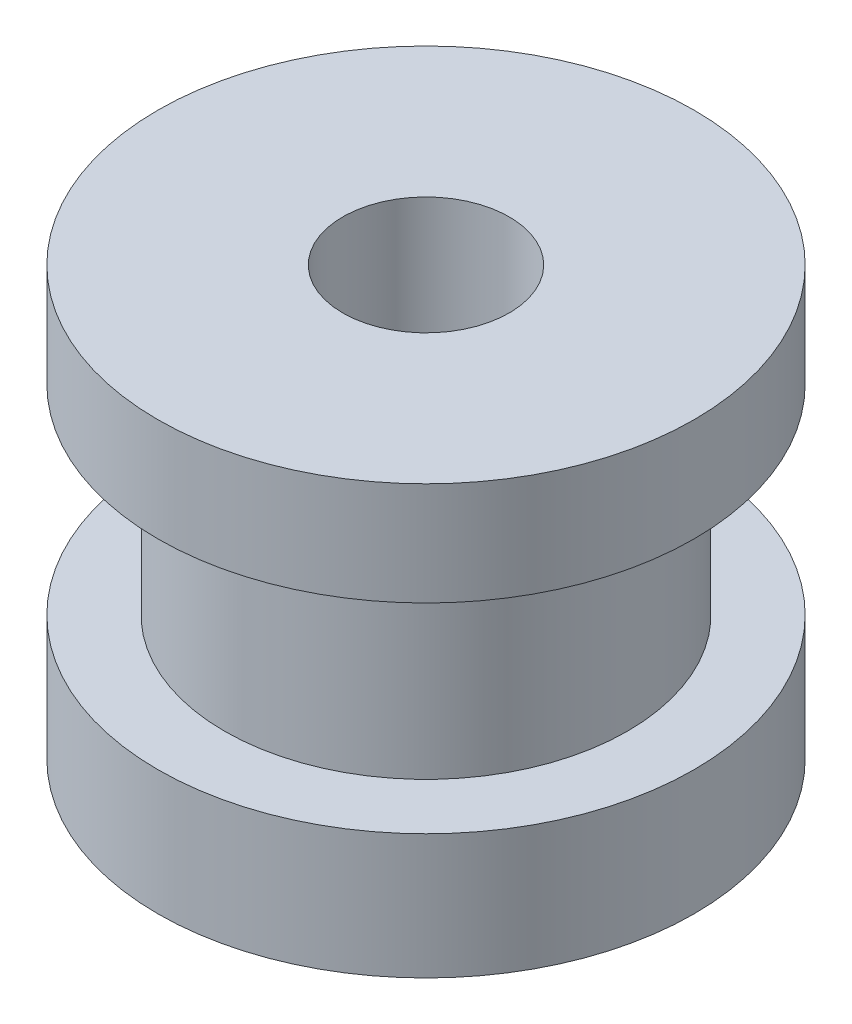
SolidWorks part; units mm, degrees
ref_plane "Front Plane" through (0, 0, 0) normal (0, 0, 1) x (1, 0, 0)
ref_plane "Top Plane" through (0, 0, 0) normal (0, 1, 0) x (1, 0, 0)
ref_plane "Right Plane" through (0, 0, 0) normal (1, 0, 0) x (0, 0, -1)
sketch "Sketch1" plane through (0, 0, 0) normal (0, 1, 0) x (1, 0, 0)
  circle A0 centre (0, 0) radius 8.05
  dimension "D1" = 16.1
extrude "Boss-Extrude1" add sketch "Sketch1" along normal blind 3.75
sketch "Sketch2" plane through (0, 3.75, 0) normal (0, 1, 0) x (1, 0, 0)
  circle A0 centre (0, 0) radius 6.05
  dimension "D1" = 12.1
extrude "Boss-Extrude2" add sketch "Sketch2" along normal blind 6
sketch "Sketch3" plane through (0, 9.75, 0) normal (0, 1, 0) x (1, 0, 0)
  circle A0 centre (0, 0) radius 8.05
  circle A1 centre (0, 0) radius 8.05 construction
extrude "Boss-Extrude3" add sketch "Sketch3" along normal blind 3.1
sketch "Sketch4" plane through (0, 0, 0) normal (0, -1, 0) x (1, 0, 0)
  circle A0 centre (0, 0) radius 2.1
  dimension "D1" = 4.2
extrude "Cut-Extrude1" cut sketch "Sketch4" against normal blind 6
sketch "Sketch5" plane through (0, 12.85, 0) normal (0, 1, 0) x (1, 0, 0)
  circle A0 centre (0, 0) radius 2.5
  dimension "D1" = 5
extrude "Cut-Extrude2" cut sketch "Sketch5" against normal blind 7
